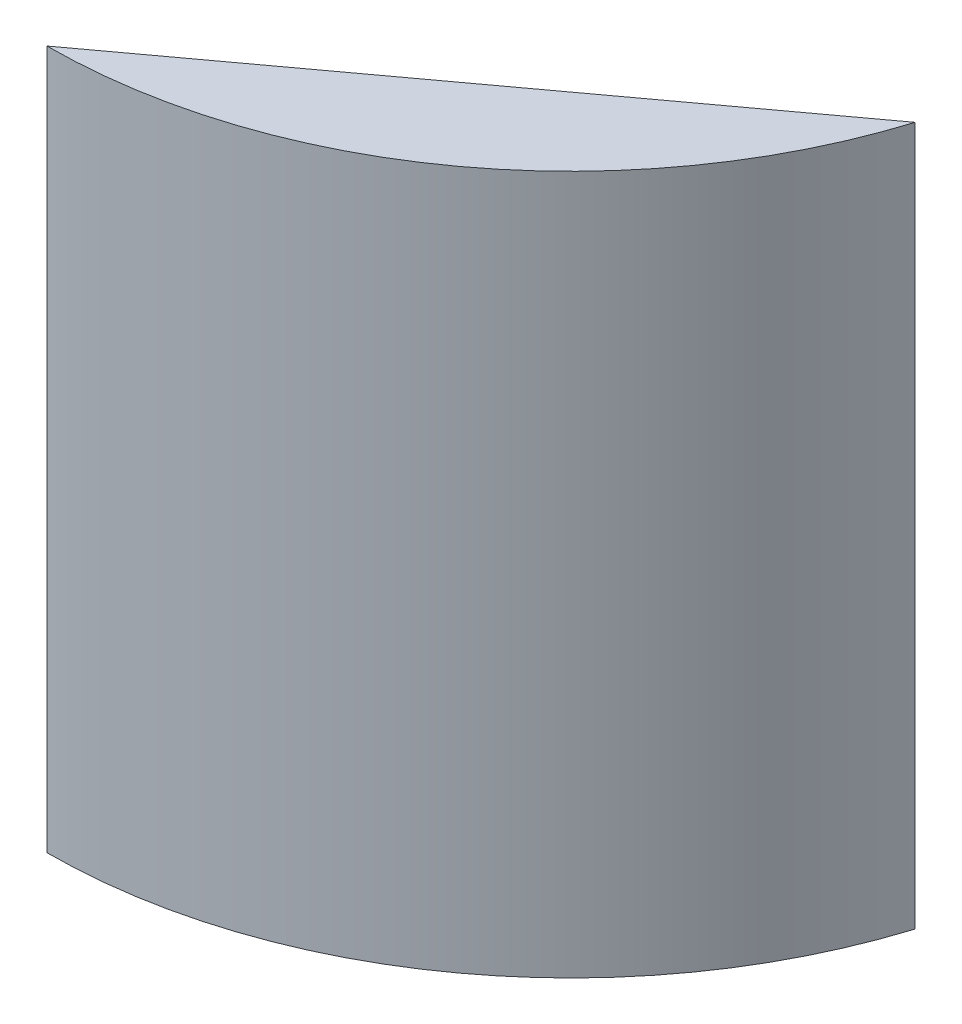
SolidWorks part; units mm, degrees
ref_plane "Front Plane" through (0, 0, 0) normal (0, 0, 1) x (1, 0, 0)
ref_plane "Top Plane" through (0, 0, 0) normal (0, 1, 0) x (1, 0, 0)
ref_plane "Right Plane" through (0, 0, 0) normal (1, 0, 0) x (0, 0, -1)
sketch "Sketch1" plane through (0, 0, 0) normal (0, 1, 0) x (1, 0, 0)
  circle A0 centre (0, 0) radius 85.725
extrude "Boss-Extrude1" add sketch "Sketch1" along normal blind 114.3
sketch "Sketch2" plane through (0, 114.3, 0) normal (0, 1, 0) x (1, 0, 0)
  line L0 (0, -85.725) -> (81.839, -25.5176)
  line L1 (81.839, -25.5176) -> (151.3047, 75.0629)
  line L2 (151.3047, 75.0629) -> (-38.5139, 115.9348)
  line L3 (-38.5139, 115.9348) -> (-149.3397, 18.864)
  line L4 (-149.3397, 18.864) -> (-68.7749, -104.5378)
  line L5 (-68.7749, -104.5378) -> (0, -85.725)
  circle A0 centre (0, 0) radius 85.725 construction
extrude "Cut-Extrude1" cut sketch "Sketch2" against normal blind 152.4
sketch "Sketch3" plane through (40.9195, 0, 55.6213) normal (-0.5926, 0, -0.8055) x (-0.8055, 0, 0.5926)
  line L0 (50.8, 0) -> (50.8, 114.3) construction
  line L1 (50.8, 0) -> (-50.8, 0) construction
  circle A0 centre (2.54, 104.14) radius 2.7781
  circle A1 centre (27.94, 104.14) radius 2.7781
  circle A2 centre (2.54, 27.94) radius 2.7781
  circle A3 centre (27.94, 27.94) radius 2.7781
  dimension "D1" = 22.86
  dimension "D2" = 76.2
  dimension "D3" = 27.94
  dimension "D4" = 76.2
  dimension "D5" = 25.4
  dimension "D6" = 25.4
extrude "Cut-Extrude2" cut sketch "Sketch3" against normal blind 7.9375
sketch "Sketch4" plane through (0, 0, 0) normal (0, -1, 0) x (-1, 0, 0)
  line L0 (-40.9195, -55.6213) -> (-50.8, -69.0517) construction
  line L1 (0, -85.725) -> (-81.839, -25.5176) construction
  circle A0 centre (-45.8598, -62.3365) radius 5.588
  arc A1 (-81.839, -25.5176) -> (0, -85.725) centre (0, 0) ccw construction
  dimension "D1" = 11.176
extrude "Cut-Extrude3" cut sketch "Sketch4" against normal blind 6.096
